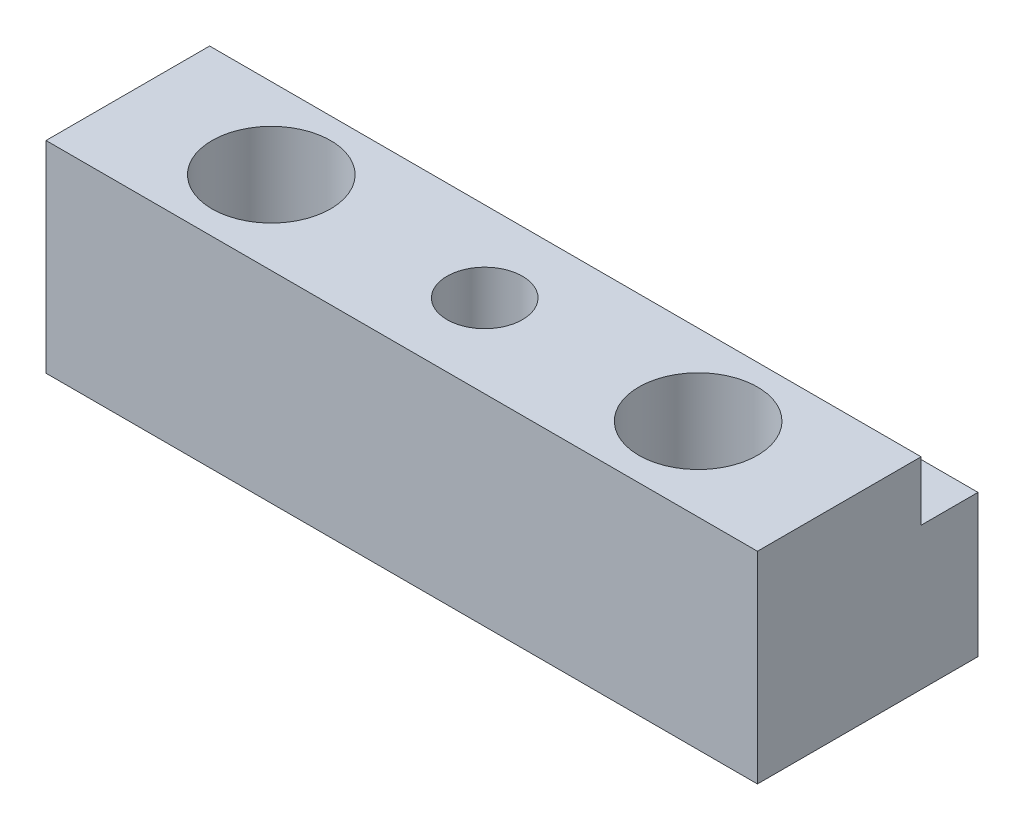
SolidWorks part; units mm, degrees
ref_plane "Front Plane" through (0, 0, 0) normal (0, 0, 1) x (1, 0, 0)
ref_plane "Top Plane" through (0, 0, 0) normal (0, 1, 0) x (1, 0, 0)
ref_plane "Right Plane" through (0, 0, 0) normal (1, 0, 0) x (0, 0, -1)
sketch "Sketch1" plane through (0, 0, 0) normal (0, 1, 0) x (1, 0, 0)
  line L1 (0, 0) -> (38.1, 0)
  line L2 (0, 0) -> (0, 11.811)
  line L3 (0, 11.811) -> (38.1, 11.811)
  line L4 (38.1, 0) -> (38.1, 11.811)
  dimension "D1" = 38.1
  dimension "D2" = 11.811
extrude "Boss-Extrude1" add sketch "Sketch1" along normal blind 10.795
sketch "Sketch2" plane through (0, 10.795, 0) normal (0, 1, 0) x (1, 0, 0)
  line L0 (38.1, 0) -> (38.1, 11.811) construction
  line L1 (0, 11.811) -> (38.1, 11.811)
  line L2 (0, 11.811) -> (0, 8.763)
  line L3 (0, 8.763) -> (38.1, 8.763)
  line L4 (38.1, 11.811) -> (38.1, 8.763)
  dimension "D1" = 3.048
extrude "Cut-Extrude1" cut sketch "Sketch2" against normal blind 3.175
hole_wizard "1/4 (0.25) Press Dowel Hole1" positions "Sketch4" profile "Sketch3" hole size "1/4" standard "ANSI Inch" end condition through all
sketch "Sketch4" plane through (0, 10.795, 0) normal (0, 1, 0) x (1, 0, 0)
  line L0 (0, 0) -> (38.1, 0) construction
  line L1 (0, 8.763) -> (0, 0) construction
  point P0 (7.62, 4.445)
  point P2 (30.48, 4.445)
  dimension "D1" = 4.445
  dimension "D2" = 22.86
  dimension "D3" = 7.62
sketch "Sketch3" plane through (7.62, 10.795, -4.445) normal (1, 0, 0) x (0, 0, 1)
  line L0 (0, 0) -> (0, 10.795)
  line L1 (0, 10.795) -> (3.175, 10.795)
  line L2 (3.175, 10.795) -> (3.175, 0)
  line L5 (3.175, 0) -> (0, 0)
  line L11 (0, -6.35) -> (0, 107.95) construction
  dimension "Thru Hole Dia." = 6.35
  dimension "Thru Hole Depth" = 10.795
hole_wizard "#10-32 Tapped Hole1" positions "Sketch8" profile "Sketch7" tap size "#10-32" standard "ANSI Inch" end condition through all
sketch "Sketch8" plane through (0, 10.795, 0) normal (0, 1, 0) x (1, 0, 0)
  line L0 (0, 0) -> (38.1, 0) construction
  line L1 (0, 8.763) -> (0, 0) construction
  point P0 (19.05, 4.445)
  dimension "D1" = 4.445
  dimension "D2" = 19.05
sketch "Sketch7" plane through (19.05, 10.795, -4.445) normal (1, 0, 0) x (0, 0, 1)
  line L0 (0, 0) -> (0, 10.795)
  line L1 (0, 10.795) -> (2.0193, 10.795)
  line L2 (2.0193, 10.795) -> (2.0193, 0)
  line L5 (2.0193, 0) -> (0, 0)
  line L11 (0, -6.35) -> (0, 107.95) construction
  dimension "Thread Major Dia." = 4.0386
  dimension "Thru Tap Drill Depth" = 10.795
